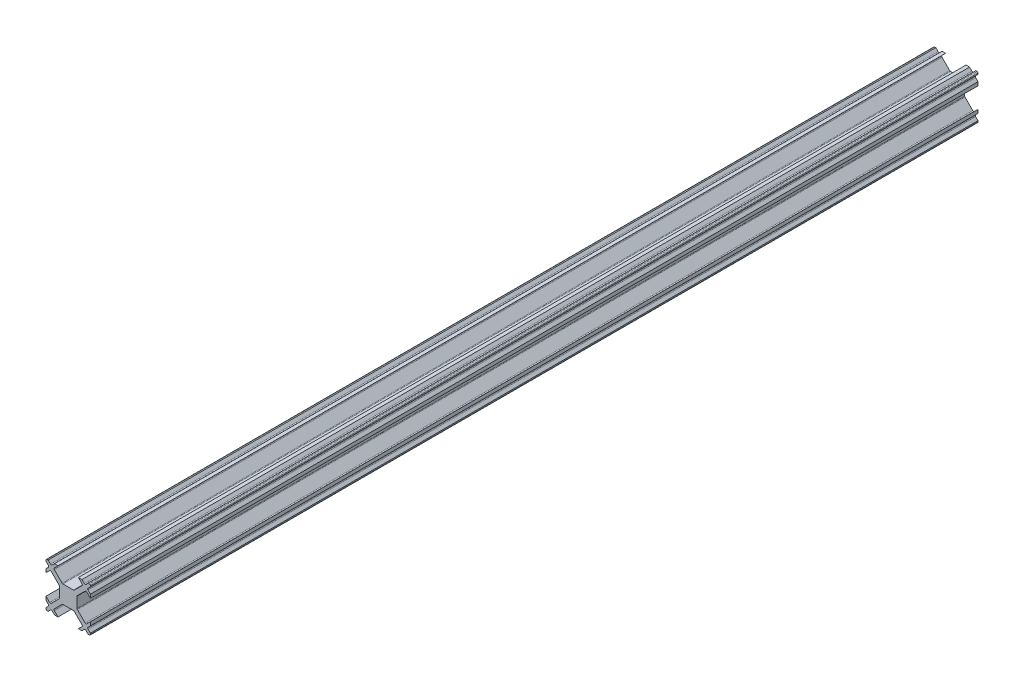
SolidWorks part; units mm, degrees
material "6063-T6"
ref_plane "Front Plane" through (0, 0, 0) normal (0, 0, 1) x (1, 0, 0)
ref_plane "Top Plane" through (0, 0, 0) normal (0, 1, 0) x (1, 0, 0)
ref_plane "Right Plane" through (0, 0, 0) normal (1, 0, 0) x (0, 0, -1)
ref_plane "Plane1" through (0, 0, 12.5) normal (0, 0, 1) x (1, 0, 0)
sketch "Sketch1" plane through (0, 0, 12.5) normal (0, 0, 1) x (1, 0, 0)
  line L0 (1.1893, 2) -> (-1.1893, 2)
  line L1 (-1.3661, 2.0732) -> (-3.1161, 3.8232)
  line L2 (-3.1161, 4.1768) -> (-2.2929, 5)
  line L3 (-2.2929, 5) -> (-3.095, 5)
  line L4 (-3.095, 5) -> (-3.6232, 4.4718)
  line L5 (-3.9768, 4.4718) -> (-4.505, 5)
  line L6 (-4.505, 5) -> (-4.75, 5)
  line L7 (-5, 4.75) -> (-5, 4.505)
  line L8 (-5, 4.505) -> (-4.4718, 3.9768)
  line L9 (-4.4718, 3.6232) -> (-5, 3.095)
  line L10 (-5, 3.095) -> (-5, 2.2929)
  line L11 (-5, 2.2929) -> (-4.1768, 3.1161)
  line L12 (-3.8232, 3.1161) -> (-2.0732, 1.3661)
  line L13 (-2, 1.1893) -> (-2, -1.1893)
  line L14 (-2.0732, -1.3661) -> (-3.8232, -3.1161)
  line L15 (-4.1768, -3.1161) -> (-5, -2.2929)
  line L16 (-5, -2.2929) -> (-5, -3.095)
  line L17 (-5, -3.095) -> (-4.4718, -3.6232)
  line L18 (-4.4718, -3.9768) -> (-5, -4.505)
  line L19 (-5, -4.505) -> (-5, -4.75)
  line L20 (-4.75, -5) -> (-4.505, -5)
  line L21 (-4.505, -5) -> (-3.9768, -4.4718)
  line L22 (-3.6232, -4.4718) -> (-3.095, -5)
  line L23 (-3.095, -5) -> (-2.2929, -5)
  line L24 (-2.2929, -5) -> (-3.1161, -4.1768)
  line L25 (-3.1161, -3.8232) -> (-1.3661, -2.0732)
  line L26 (-1.1893, -2) -> (1.1893, -2)
  line L27 (1.3661, -2.0732) -> (3.1161, -3.8232)
  line L28 (3.1161, -4.1768) -> (2.2929, -5)
  line L29 (2.2929, -5) -> (3.095, -5)
  line L30 (3.095, -5) -> (3.6232, -4.4718)
  line L31 (3.9768, -4.4718) -> (4.505, -5)
  line L32 (4.505, -5) -> (4.75, -5)
  line L33 (5, -4.75) -> (5, -4.505)
  line L34 (5, -4.505) -> (4.4718, -3.9768)
  line L35 (4.4718, -3.6232) -> (5, -3.095)
  line L36 (5, -3.095) -> (5, -2.2929)
  line L37 (5, -2.2929) -> (4.1768, -3.1161)
  line L38 (3.8232, -3.1161) -> (2.0732, -1.3661)
  line L39 (2, -1.1893) -> (2, 1.1893)
  line L40 (2.0732, 1.3661) -> (3.8232, 3.1161)
  line L41 (4.1768, 3.1161) -> (5, 2.2929)
  line L42 (5, 2.2929) -> (5, 3.095)
  line L43 (5, 3.095) -> (4.4718, 3.6232)
  line L44 (4.4718, 3.9768) -> (5, 4.505)
  line L45 (5, 4.505) -> (5, 4.75)
  line L46 (4.75, 5) -> (4.505, 5)
  line L47 (4.505, 5) -> (3.9768, 4.4718)
  line L48 (3.6232, 4.4718) -> (3.095, 5)
  line L49 (3.095, 5) -> (2.2929, 5)
  line L50 (2.2929, 5) -> (3.1161, 4.1768)
  line L51 (3.1161, 3.8232) -> (1.3661, 2.0732)
  arc A0 (1.3661, 2.0732) -> (1.1893, 2) centre (1.1893, 2.25) cw
  arc A1 (-1.1893, 2) -> (-1.3661, 2.0732) centre (-1.1893, 2.25) cw
  arc A2 (-3.1161, 3.8232) -> (-3.1161, 4.1768) centre (-2.9393, 4) cw
  arc A3 (-3.6232, 4.4718) -> (-3.9768, 4.4718) centre (-3.8, 4.6485) cw
  arc A4 (-4.75, 5) -> (-5, 4.75) centre (-4.75, 4.75) ccw
  arc A5 (-4.4718, 3.9768) -> (-4.4718, 3.6232) centre (-4.6485, 3.8) cw
  arc A6 (-4.1768, 3.1161) -> (-3.8232, 3.1161) centre (-4, 2.9393) cw
  arc A7 (-2.0732, 1.3661) -> (-2, 1.1893) centre (-2.25, 1.1893) cw
  arc A8 (-2, -1.1893) -> (-2.0732, -1.3661) centre (-2.25, -1.1893) cw
  arc A9 (-3.8232, -3.1161) -> (-4.1768, -3.1161) centre (-4, -2.9393) cw
  arc A10 (-4.4718, -3.6232) -> (-4.4718, -3.9768) centre (-4.6485, -3.8) cw
  arc A11 (-5, -4.75) -> (-4.75, -5) centre (-4.75, -4.75) ccw
  arc A12 (-3.9768, -4.4718) -> (-3.6232, -4.4718) centre (-3.8, -4.6485) cw
  arc A13 (-3.1161, -4.1768) -> (-3.1161, -3.8232) centre (-2.9393, -4) cw
  arc A14 (-1.3661, -2.0732) -> (-1.1893, -2) centre (-1.1893, -2.25) cw
  arc A15 (1.1893, -2) -> (1.3661, -2.0732) centre (1.1893, -2.25) cw
  arc A16 (3.1161, -3.8232) -> (3.1161, -4.1768) centre (2.9393, -4) cw
  arc A17 (3.6232, -4.4718) -> (3.9768, -4.4718) centre (3.8, -4.6485) cw
  arc A18 (4.75, -5) -> (5, -4.75) centre (4.75, -4.75) ccw
  arc A19 (4.4718, -3.9768) -> (4.4718, -3.6232) centre (4.6485, -3.8) cw
  arc A20 (4.1768, -3.1161) -> (3.8232, -3.1161) centre (4, -2.9393) cw
  arc A21 (2.0732, -1.3661) -> (2, -1.1893) centre (2.25, -1.1893) cw
  arc A22 (2, 1.1893) -> (2.0732, 1.3661) centre (2.25, 1.1893) cw
  arc A23 (3.8232, 3.1161) -> (4.1768, 3.1161) centre (4, 2.9393) cw
  arc A24 (4.4718, 3.6232) -> (4.4718, 3.9768) centre (4.6485, 3.8) cw
  arc A25 (5, 4.75) -> (4.75, 5) centre (4.75, 4.75) ccw
  arc A26 (3.9768, 4.4718) -> (3.6232, 4.4718) centre (3.8, 4.6485) cw
  arc A27 (3.1161, 4.1768) -> (3.1161, 3.8232) centre (2.9393, 4) cw
extrude "Boss-Extrude1" add sketch "Sketch1" against normal blind 200
